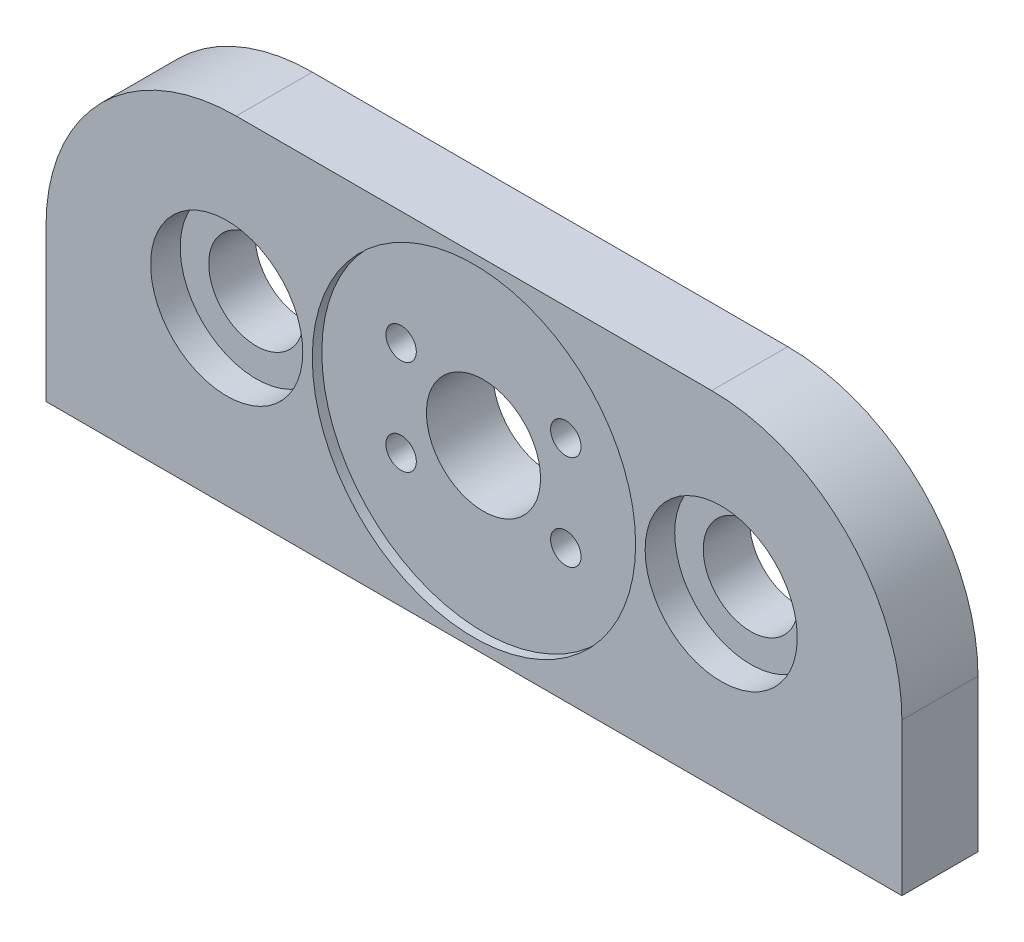
SolidWorks part; units mm, degrees
ref_plane "Front Plane" through (0, 0, 0) normal (0, 0, 1) x (1, 0, 0)
ref_plane "Top Plane" through (0, 0, 0) normal (0, 1, 0) x (1, 0, 0)
ref_plane "Right Plane" through (0, 0, 0) normal (1, 0, 0) x (0, 0, -1)
sketch "Sketch1" plane through (0, 0, 0) normal (0, 1, 0) x (1, 0, 0)
  line L1 (0, 0) -> (-45, 0)
  line L2 (0, 0) -> (0, 4)
  line L3 (0, 4) -> (-45, 4)
  line L4 (-45, 0) -> (-45, 4)
  dimension "D1" = 45
  dimension "D2" = 4
extrude "Boss-Extrude1" add sketch "Sketch1" along normal blind 18
sketch "Sketch2" plane through (0, 0, 0) normal (0, 0, 1) x (1, 0, 0)
  line L0 (-22.5, 18) -> (-22.5, 0) construction
  line L1 (-45, 18) -> (0, 18) construction
  line L2 (-45, 0) -> (0, 0) construction
  circle A0 centre (-22.5, 9) radius 8.5
  dimension "D1" = 17
extrude "Cut-Extrude2" cut sketch "Sketch2" against normal blind 0.5
sketch "Sketch3" plane through (0, 0, -0.5) normal (0, 0, 1) x (1, 0, 0)
  line L0 (-22.5, 17.5) -> (-22.5, 0.5) construction
  circle A0 centre (-22.5, 9) radius 8.5 construction
  circle A1 centre (-22.5, 9) radius 8.5 construction
  circle A2 centre (-22.5, 9) radius 3
  dimension "D1" = 6
extrude "Cut-Extrude3" cut sketch "Sketch3" against normal through all
sketch "Sketch4" plane through (0, 0, 0) normal (0, 0, 1) x (1, 0, 0)
  line L0 (-22.5, 18) -> (-22.5, 0) construction
  line L1 (-45, 18) -> (0, 18) construction
  line L2 (-45, 0) -> (0, 0) construction
  circle A0 centre (-35.5, 9) radius 2.5
  circle A1 centre (-9.5, 9) radius 2.5
  dimension "D1" = 5
  dimension "D2" = 13
  dimension "D3" = 9
extrude "Cut-Extrude4" cut sketch "Sketch4" against normal through all contours A0 | A1
sketch "Sketch6" plane through (0, 0, -0.5) normal (0, 0, 1) x (1, 0, 0)
  circle A0 centre (-22.5, 9) radius 5
  circle A2 centre (-18.1699, 11.5) radius 0.8
  circle A3 centre (-18.1699, 6.5) radius 0.8
  circle A5 centre (-26.8301, 6.5) radius 0.8
  circle A6 centre (-26.8301, 11.5) radius 0.8
  point P17 (-22.5, 9)
  dimension "D1" = 10
extrude "Cut-Extrude6" cut sketch "Sketch6" against normal through all
fillet "Fillet1" radius 10 2 edges at (0, 18, -2) (-45, 18, -2)
sketch "Sketch7" plane through (0, 0, 0) normal (0, 0, 1) x (1, 0, 0)
  line L0 (-35.5, 11.5) -> (-35.5, 6.5) construction
  line L1 (-22.5, 18) -> (-22.5, 0) construction
  line L2 (-35, 18) -> (-10, 18) construction
  line L3 (-45, 0) -> (0, 0) construction
  circle A0 centre (-35.5, 9) radius 2.5 construction
  circle A1 centre (-35.5, 9) radius 4
  circle A2 centre (-9.5, 9) radius 4
  dimension "D1" = 8
extrude "Cut-Extrude7" cut sketch "Sketch7" against normal blind 1.555
sketch "Sketch8" plane through (0, 0, 0) normal (0, -1, 0) x (1, 0, 0)
  line L0 (-22.5, 0) -> (-22.5, -4) construction
  line L1 (-45, 0) -> (0, 0) construction
  line L2 (0, -4) -> (-45, -4) construction
  line L3 (-22.5, -2) -> (-45.9583, -2) construction
  line L4 (-5.2173, -2) -> (-4.4173, -0.6144)
  line L5 (-39.7827, -2) -> (-40.5827, -0.6144)
  line L6 (-40.5827, -0.6144) -> (-42.1827, -0.6144)
  line L7 (-42.1827, -0.6144) -> (-42.9827, -2)
  line L8 (-42.9827, -2) -> (-42.1827, -3.3856)
  line L9 (-42.1827, -3.3856) -> (-40.5827, -3.3856)
  line L10 (-40.5827, -3.3856) -> (-39.7827, -2)
  line L11 (-4.4173, -3.3856) -> (-5.2173, -2)
  line L12 (-2.8173, -3.3856) -> (-4.4173, -3.3856)
  line L13 (-2.0173, -2) -> (-2.8173, -3.3856)
  line L14 (-2.8173, -0.6144) -> (-2.0173, -2)
  line L15 (-4.4173, -0.6144) -> (-2.8173, -0.6144)
  circle A0 centre (-41.3827, -2) radius 1.3856 construction
  dimension "D1" = 3.2
extrude "Cut-Extrude8" cut sketch "Sketch8" against normal blind 1.3
sketch "Sketch9" plane through (0, 1.3, 0) normal (0, -1, 0) x (1, 0, 0)
  line L0 (-42.9827, -2) -> (-39.7827, -2) construction
  line L3 (-42.1827, -0.6144) -> (-40.5827, -3.3856) construction
  circle A0 centre (-41.3827, -2) radius 0.9
  dimension "D1" = 1.8
sketch "Sketch10" plane through (0, 1.3, 0) normal (0, -1, 0) x (1, 0, 0)
  line L0 (-4.4173, -0.6144) -> (-2.8173, -3.3856) construction
  line L1 (-2.8173, -3.3856) -> (-2.0173, -2) construction
  line L2 (-2.0173, -2) -> (-5.2173, -2) construction
  circle A0 centre (-3.6173, -2) radius 0.9
  dimension "D1" = 1.8
extrude "Cut-Extrude9" cut sketch "Sketch9" against normal blind 5
extrude "Cut-Extrude10" cut sketch "Sketch10" against normal blind 5
chamfer "Chamfer1" distance 0.7 distance2 0.7 4 edges at (-17.3699, 6.5, -4) (-26.0301, 6.5, -4) (-26.0301, 11.5, -4) (-17.3699, 11.5, -4)
